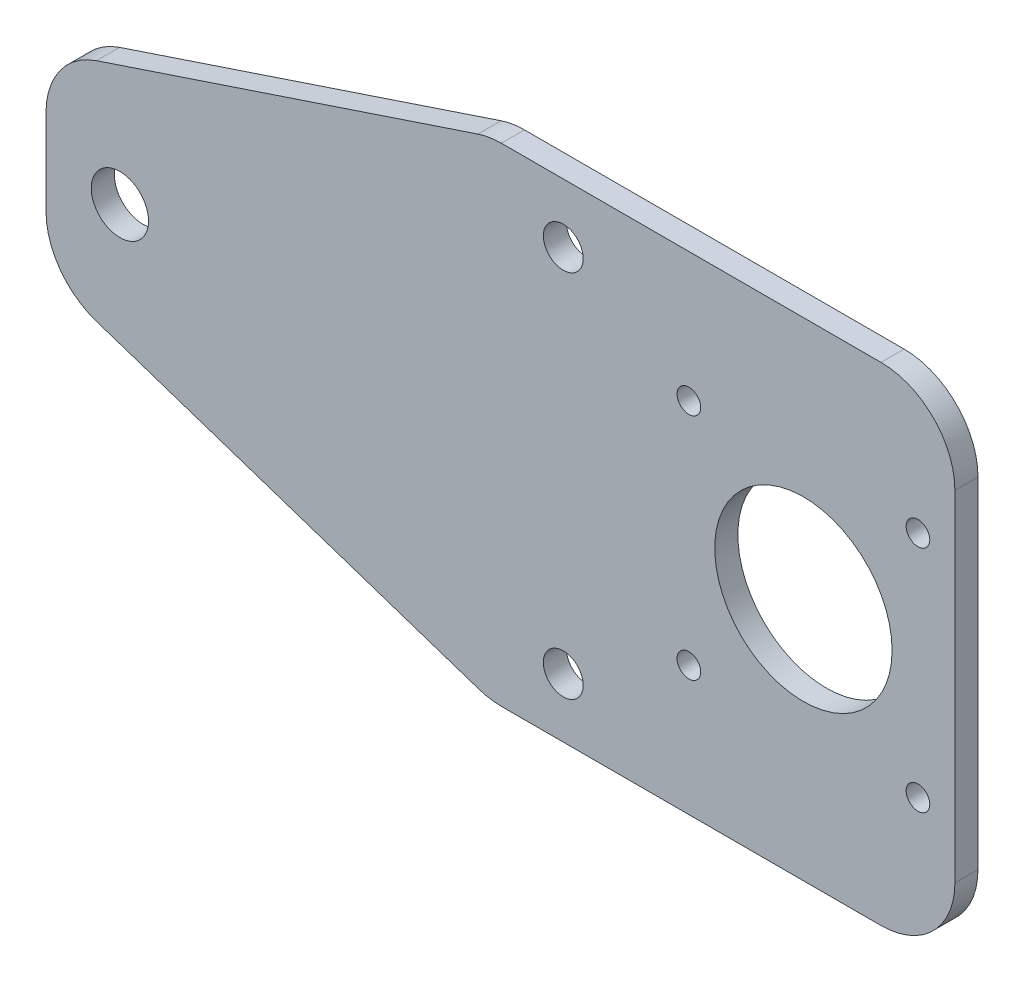
SolidWorks part; units mm, degrees
ref_plane "Front Plane" through (0, 0, 0) normal (0, 0, 1) x (1, 0, 0)
ref_plane "Top Plane" through (0, 0, 0) normal (0, 1, 0) x (1, 0, 0)
ref_plane "Right Plane" through (0, 0, 0) normal (1, 0, 0) x (0, 0, -1)
sketch "Model" plane through (0, 0, 0) normal (0, 0, 1) x (1, 0, 0)
  line L0 (79.9458, 0) -> (80.0523, -0.044) construction
  line L1 (-0.0635, 46) -> (-0.0635, 20)
  line L2 (59.9365, 66) -> (122.9365, 66)
  line L3 (122.9365, 66) -> (122.9365, 0)
  line L4 (122.9365, 0) -> (60, 0)
  line L5 (-0.0635, 46) -> (59.9365, 66)
  line L6 (-0.0635, 20) -> (60, 0)
  circle A0 centre (69.9365, 8) radius 2.7
  circle A1 centre (9.9365, 33) radius 3.875
  circle A2 centre (69.9365, 58) radius 2.7
  circle A3 centre (102.4365, 33) radius 12
  circle A4 centre (86.9365, 48.5) radius 1.6
  circle A5 centre (117.9365, 48.5) radius 1.6
  circle A6 centre (86.9365, 17.5) radius 1.6
  circle A7 centre (117.9365, 17.5) radius 1.6
  dimension "D1" = 31
  dimension "D4" = 50
  dimension "D5" = 5.4
  dimension "D6" = 60
  dimension "D8" = 24
  dimension "D12" = 20
  dimension "D13" = 20
  dimension "D14" = 66
  dimension "D15" = 9.9365
  dimension "D16" = 7.75
  dimension "D17" = 25
  dimension "D18" = 3.2
  dimension "D21" = 122.9365
  dimension "D7" = 60
  dimension "D11" = 33
  dimension "D2" = 31
  dimension "D3" = 60
  dimension "D9" = 15.5
  dimension "D10" = 15.5
  dimension "D19" = 62.9365
  dimension "D20" = 17
  dimension "D22" = 63.3058
extrude "Boss-Extrude1" add sketch "Model" along normal blind 3.125
fillet "Fillet1" radius 10 6 edges at (60, 0, 1.5625) (59.9365, 66, 1.5625) (-0.0635, 46, 1.5625) (-0.0635, 20, 1.5625) (122.9365, 0, 1.5625) (122.9365, 66, 1.5625)
